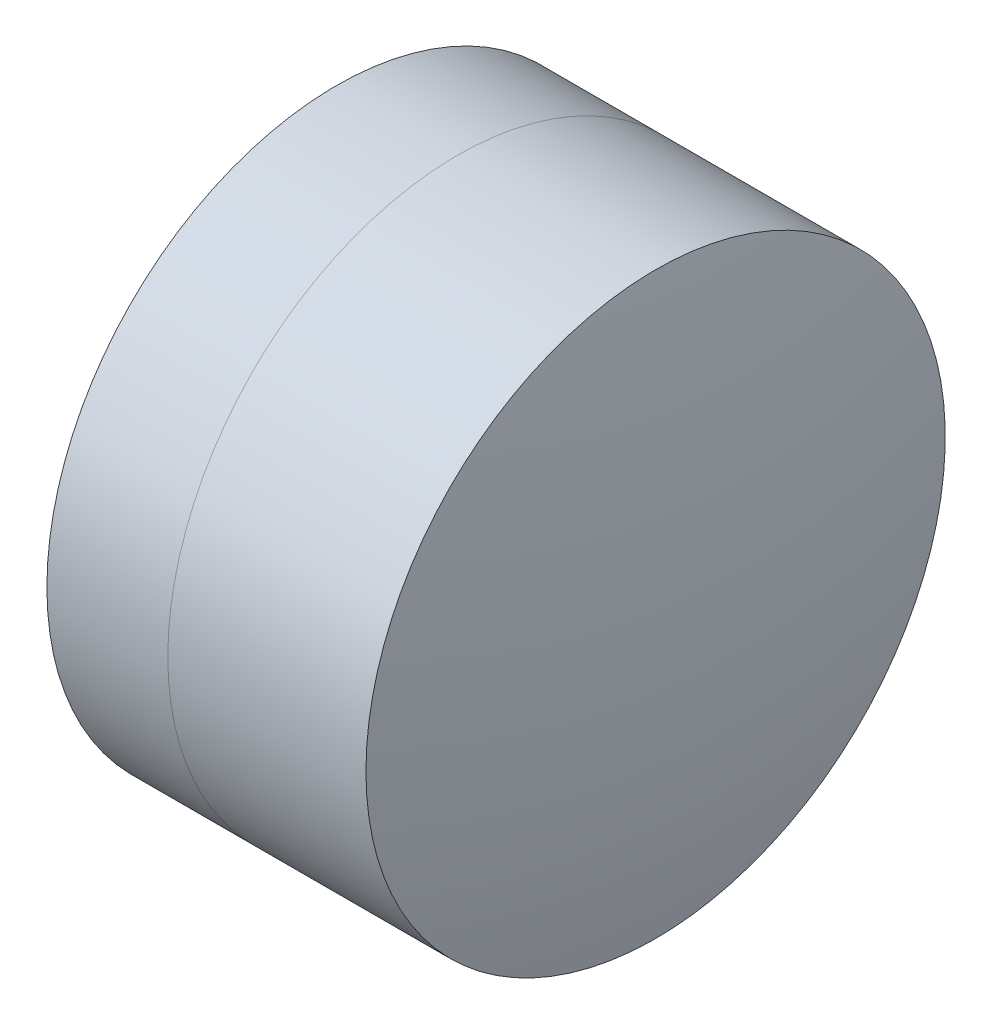
SolidWorks part; units mm, degrees
ref_plane "前视基准面" through (0, 0, 0) normal (0, 0, 1) x (1, 0, 0)
ref_plane "上视基准面" through (0, 0, 0) normal (0, 1, 0) x (1, 0, 0)
ref_plane "右视基准面" through (0, 0, 0) normal (1, 0, 0) x (0, 0, -1)
sketch "草图1" plane through (0, 0, 0) normal (0, 1, 0) x (1, 0, 0)
  line L0 (-0.8161, 0) -> (8.3573, 0) construction
  line L1 (4.1611, -3.15) -> (5.4757, -3.15)
  line L2 (4.1611, 3.15) -> (5.4757, 3.15)
  arc A0 (5.4757, -3.15) -> (5.4757, 3.15) centre (1.0946, 0) ccw
  arc A1 (4.1611, 3.15) -> (4.1611, -3.15) centre (11.7146, 0) ccw
  point P4 (7.4117, 0)
  point P6 (8.3573, 0)
  point P10 (3.5306, 0)
  point P11 (6.4906, 0)
  dimension "D3" = 8.184
  dimension "D4" = 5.396
  dimension "D1" = 3.15
  dimension "D2" = 3.15
  dimension "D5" = 2.96
revolve "旋转1" add sketch "草图1" angle 360 about L0
sketch "草图2" plane through (0, 0, 0) normal (0, 1, 0) x (1, 0, 0)
  line L0 (-0.5519, 0) -> (10.269, 0) construction
  line L2 (5.4757, 3.15) -> (7.6303, 3.15)
  line L3 (5.4757, -3.15) -> (7.6303, -3.15)
  arc A0 (7.6303, -3.15) -> (7.6303, 3.15) centre (-6.7804, 0) ccw
  arc A1 (5.4757, -3.15) -> (5.4757, 3.15) centre (1.0946, 0) ccw construction
  arc A2 (5.4757, -3.15) -> (5.4757, 3.15) centre (1.0946, 0) ccw
  point P4 (6.4906, 0)
  point P8 (7.9706, 0)
  point P9 (10.269, 0)
  dimension "D1" = 14.751
  dimension "D2" = 1.48
revolve "旋转3" add sketch "草图2" angle 360 about L0
